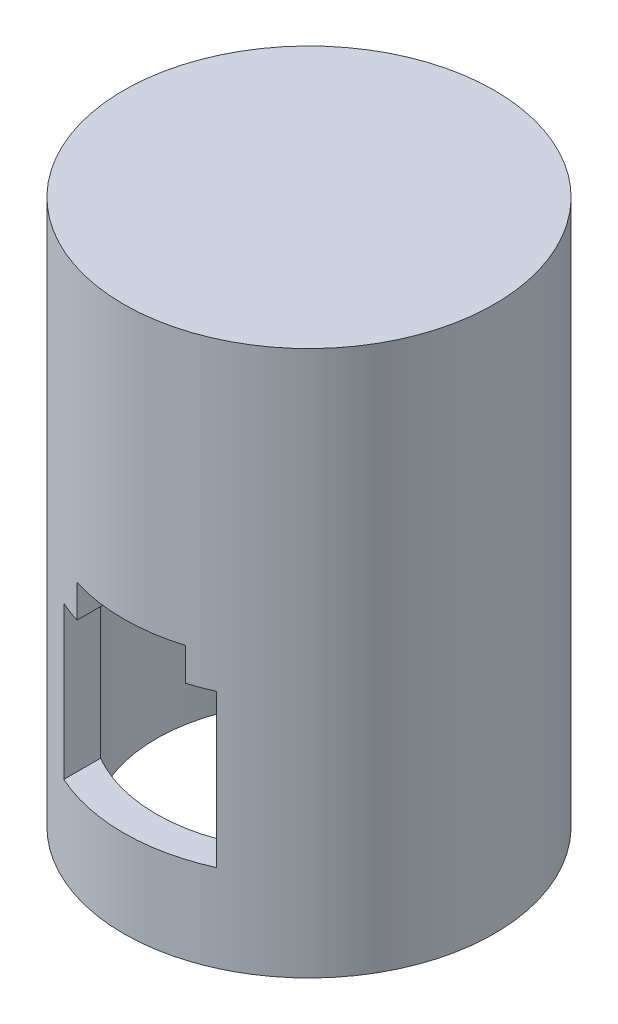
SolidWorks part; units mm, degrees
ref_plane "Front Plane" through (0, 0, 0) normal (0, 0, 1) x (1, 0, 0)
ref_plane "Top Plane" through (0, 0, 0) normal (0, 1, 0) x (1, 0, 0)
ref_plane "Right Plane" through (0, 0, 0) normal (1, 0, 0) x (0, 0, -1)
sketch "Sketch1" plane through (0, 0, 0) normal (0, 1, 0) x (1, 0, 0)
  circle A0 centre (0, 0) radius 17
extrude "Boss-Extrude1" add sketch "Sketch1" along normal blind 30
sketch "Sketch2" plane through (0, 30, 0) normal (0, 1, 0) x (1, 0, 0)
  circle A0 centre (0, 0) radius 14
extrude "Cut-Extrude1" cut sketch "Sketch2" against normal blind 30
sketch "Sketch3" plane through (0, 0, 0) normal (0, 0, 1) x (1, 0, 0)
  line L0 (-17, 0) -> (17, 0) construction
  line L1 (7, 22) -> (-7, 22)
  line L2 (7, 22) -> (7, 8)
  line L3 (7, 8) -> (-7, 8)
  line L4 (-7, 22) -> (-7, 8)
  line L5 (7, 22) -> (-7, 8) construction
  line L6 (7, 8) -> (-7, 22) construction
  line L7 (17, 0) -> (17, 30) construction
  point P0 (0, 15)
  dimension "D1" = 7
  dimension "D2" = 7
  dimension "D3" = 15
  dimension "D4" = 17
extrude "Cut-Extrude2" cut sketch "Sketch3" against normal through all both and the other way through all
sketch "Sketch4" plane through (0, 30, 0) normal (0, 1, 0) x (1, 0, 0)
  circle A0 centre (0, 0) radius 17
extrude "Boss-Extrude2" add sketch "Sketch4" along normal blind 20
sketch "Sketch6" plane through (0, 0, 0) normal (0, 0, 1) x (1, 0, 0)
  line L0 (-7, 22) -> (7, 22) construction
  line L1 (4.951, 25) -> (-5.049, 25)
  line L2 (4.951, 25) -> (4.951, 19)
  line L3 (4.951, 19) -> (-5.049, 19)
  line L4 (-5.049, 25) -> (-5.049, 19)
  line L5 (4.951, 25) -> (-5.049, 19) construction
  line L6 (4.951, 19) -> (-5.049, 25) construction
  point P0 (-0.049, 22)
  point P7 (0, 22)
  dimension "D1" = 5
  dimension "D2" = 3
  dimension "D3" = 0
extrude "Cut-Extrude3" cut sketch "Sketch6" against normal through all both and the other way through all
